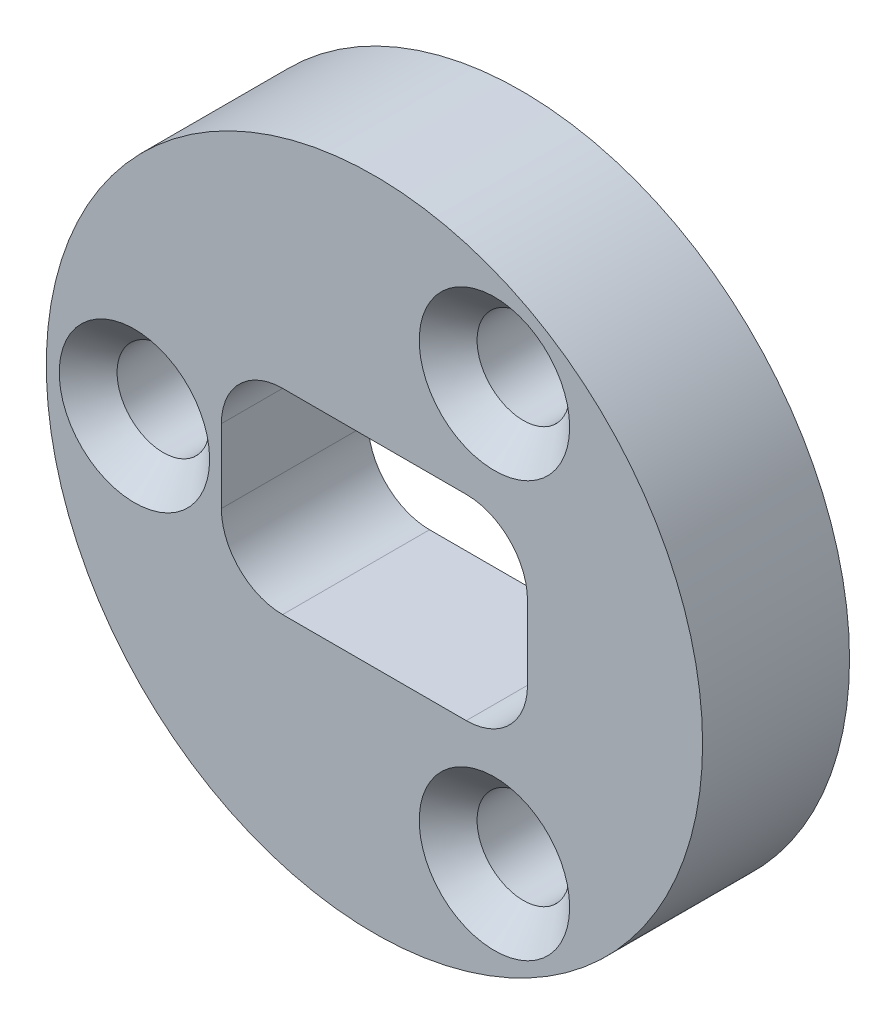
SolidWorks part; units mm, degrees
ref_plane "Front Plane" through (0, 0, 0) normal (0, 0, 1) x (1, 0, 0)
ref_plane "Top Plane" through (0, 0, 0) normal (0, 1, 0) x (1, 0, 0)
ref_plane "Right Plane" through (0, 0, 0) normal (1, 0, 0) x (0, 0, -1)
sketch "Sketch1" plane through (0, 0, 0) normal (0, 0, 1) x (1, 0, 0)
  circle A0 centre (0, 0) radius 8.509
  dimension "D1" = 17.018
extrude "Boss-Extrude1" add sketch "Sketch1" along normal blind 3.81
ref_plane "Plane1" through (0, 0, 3.81) normal (0, 0, 1) x (1, 0, 0)
sketch "Sketch2" plane through (0, 0, 3.81) normal (0, 0, 1) x (1, 0, 0)
  line L0 (-8.509, 0) -> (8.509, 0) construction
  circle A0 centre (0, 0) radius 6.223 construction
  circle A1 centre (0, 0) radius 8.509 construction
  circle A2 centre (-6.223, 0) radius 1.143
  circle A3 centre (3.1115, 5.3893) radius 1.143
  circle A4 centre (3.1115, -5.3893) radius 1.143
  point P16 (0, 0)
  dimension "D1" = 12.446
  dimension "D2" = 2.286
  dimension "D4" = 3.1115
  dimension "D5" = 5.3893
  dimension "D3" = 3
sketch "Sketch3" plane through (0, 0, 3.81) normal (0, 0, 1) x (1, 0, 0)
  line L0 (-8.509, 0) -> (8.509, 0) construction
  line L1 (-3.9688, 2.54) -> (3.9688, 2.54)
  line L2 (-3.9688, 2.54) -> (-3.9688, -2.54)
  line L3 (-3.9688, -2.54) -> (3.9687, -2.54)
  line L4 (3.9688, 2.54) -> (3.9687, -2.54)
  circle A0 centre (0, 0) radius 8.509 construction
  dimension "D1" = 5.08
  dimension "D2" = 3.9688
  dimension "D3" = 7.9375
  dimension "D4" = 2.54
extrude "Cut-Extrude2" cut sketch "Sketch3" against normal blind 3.81
hole_wizard "M2 Clearance Hole1" positions "Sketch4" profile "Sketch5" hole size "M2" standard "ANSI Metric" end condition through all
sketch "Sketch4" plane through (0, 0, 3.81) normal (0, 0, 1) x (1, 0, 0)
  point P0 (-6.223, 0)
  point P3 (3.1115, 5.3893)
  point P6 (3.1115, -5.3893)
sketch "Sketch5" plane through (-6.223, 0, 3.81) normal (1, 0, 0) x (0, -1, 0)
  line L0 (0, 0) -> (0, 3.81)
  line L1 (0, 3.81) -> (1.2, 3.81)
  line L2 (1.2, 3.81) -> (1.2, 0)
  line L5 (1.2, 0) -> (0, 0)
  line L11 (0, -6.35) -> (0, 107.95) construction
  dimension "Thru Hole Dia." = 2.4
  dimension "Thru Hole Depth" = 3.81
fillet "Fillet1" radius 1.5875 4 edges at (3.9687, -2.54, 1.905) (-3.9688, -2.54, 1.905) (3.9688, 2.54, 1.905) (-3.9688, 2.54, 1.905)
chamfer "Chamfer1" distance 0.75 angle 45 3 edges at (4.3115, -5.3893, 3.81) (-5.023, 0, 3.81) (4.3115, 5.3893, 3.81)
